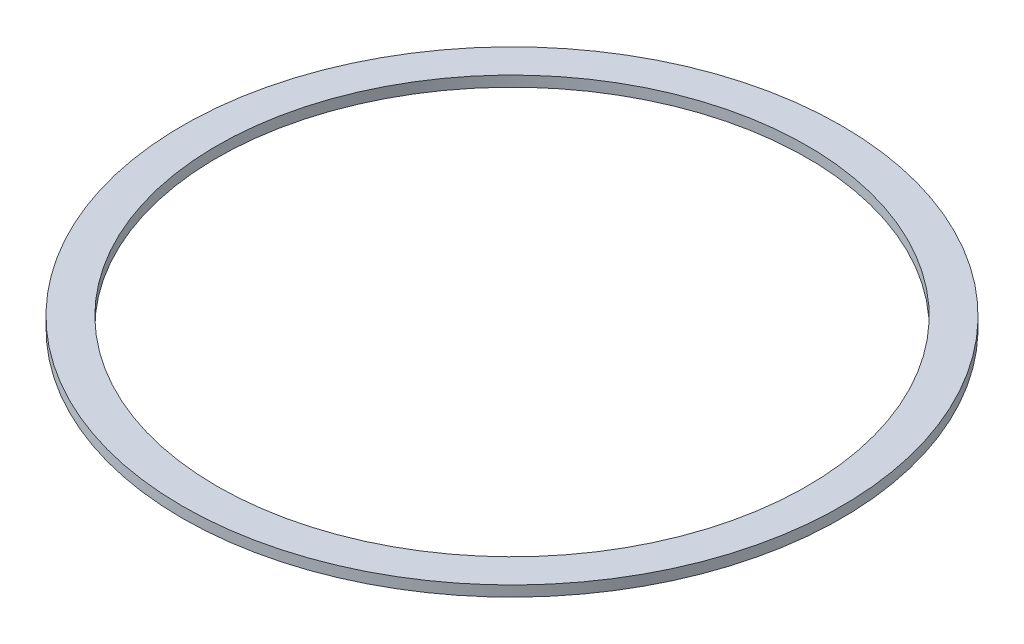
SolidWorks part; units mm, degrees
ref_plane "Front Plane" through (0, 0, 0) normal (0, 0, 1) x (1, 0, 0)
ref_plane "Top Plane" through (0, 0, 0) normal (0, 1, 0) x (1, 0, 0)
ref_plane "Right Plane" through (0, 0, 0) normal (1, 0, 0) x (0, 0, -1)
sketch "Sketch1" plane through (0, 0, 0) normal (0, 1, 0) x (1, 0, 0)
  circle A0 centre (0, 0) radius 88.9
  circle A1 centre (0, 0) radius 99.314
  dimension "D1" = 177.8
  dimension "D2" = 198.628
extrude "Boss-Extrude1" add sketch "Sketch1" along normal blind 3.175
equation "\"2x3.5\"=3.60815"
